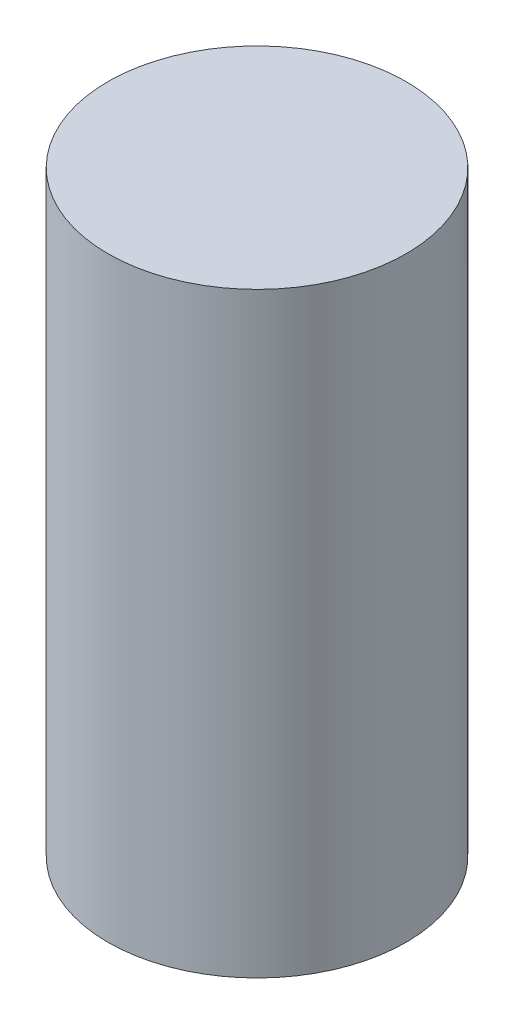
SolidWorks part; units mm, degrees
ref_plane "Front Plane" through (0, 0, 0) normal (0, 0, 1) x (1, 0, 0)
ref_plane "Top Plane" through (0, 0, 0) normal (0, 1, 0) x (1, 0, 0)
ref_plane "Right Plane" through (0, 0, 0) normal (1, 0, 0) x (0, 0, -1)
sketch "Sketch1" plane through (0, 0, 0) normal (0, 1, 0) x (1, 0, 0)
  circle A0 centre (0, 0) radius 100
  dimension "D1" = 200
extrude "Boss-Extrude1" add sketch "Sketch1" along normal blind 400
